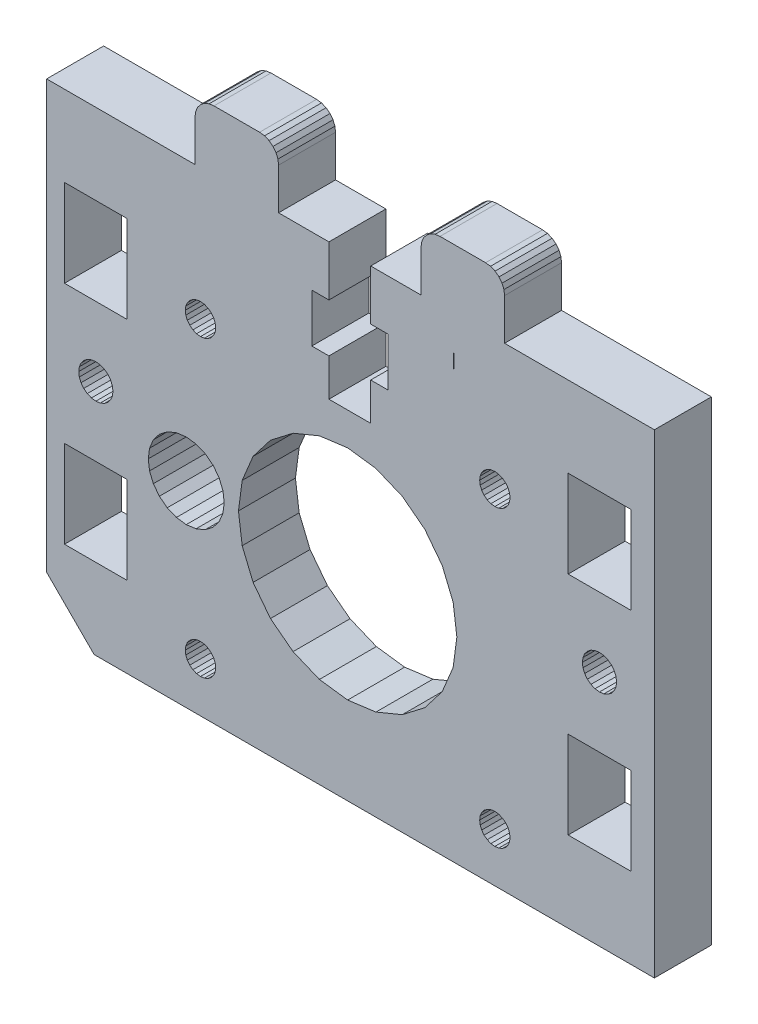
SolidWorks part; units mm, degrees
material "Maple"
ref_plane "Front Plane" through (0, 0, 0) normal (0, 0, 1) x (1, 0, 0)
ref_plane "Top Plane" through (0, 0, 0) normal (0, 1, 0) x (1, 0, 0)
ref_plane "Right Plane" through (0, 0, 0) normal (1, 0, 0) x (0, 0, -1)
sketch "Sketch1" plane through (0, 0, 0) normal (0, 0, 1) x (1, 0, 0)
  line L7685 (301.9537, 85.0925) -> (301.9537, 79.7925)
  line L7686 (267.8287, 40.0925) -> (272.8287, 35.0925)
  line L7687 (297.5537, 74.6925) -> (295.7537, 74.6925)
  line L7688 (316.0537, 85.0925) -> (316.0537, 89.4425)
  line L7689 (295.7537, 74.6925) -> (295.7537, 79.7925)
  line L7690 (307.2537, 85.0925) -> (301.9537, 85.0925)
  line L7691 (292.2537, 85.0925) -> (292.2537, 89.4425)
  line L7692 (329.3486, 76.5925) -> (329.3486, 67.3925)
  line L7693 (295.7537, 79.7925) -> (297.5537, 79.7925)
  line L7694 (329.3486, 67.3925) -> (322.7487, 67.3925)
  line L7695 (267.8287, 85.0925) -> (267.8287, 40.0925)
  line L7696 (301.9537, 79.7925) -> (303.7537, 79.7925)
  line L7697 (297.5537, 85.0925) -> (292.2537, 85.0925)
  line L7698 (303.7537, 74.6925) -> (301.9537, 74.6925)
  line L7699 (297.5537, 79.7925) -> (297.5537, 85.0925)
  line L7700 (303.7537, 79.7925) -> (303.7537, 74.6925)
  line L7701 (322.7487, 67.3925) -> (322.7487, 76.5925)
  line L7702 (322.7487, 76.5925) -> (329.3486, 76.5925)
  line L7703 (301.9537, 70.7425) -> (297.5537, 70.7425)
  line L7704 (297.5537, 70.7425) -> (297.5537, 74.6925)
  line L7705 (288.4205, 52.8161) -> (288.0287, 55.7925)
  line L7706 (283.6146, 72.838) -> (284.0287, 72.8925)
  line L7707 (301.9537, 74.6925) -> (301.9537, 70.7425)
  line L7708 (316.0537, 89.4425) -> (315.9855, 89.9601)
  line L7709 (315.9855, 89.9601) -> (315.7857, 90.4425)
  line L7710 (315.7857, 90.4425) -> (315.4679, 90.8567)
  line L7711 (315.4679, 90.8567) -> (315.0537, 91.1746)
  line L7712 (315.0537, 91.1746) -> (314.5713, 91.3744)
  line L7713 (314.0537, 91.4425) -> (309.2537, 91.4425)
  line L7714 (314.5713, 91.3744) -> (314.0537, 91.4425)
  line L7715 (283.4537, 89.4425) -> (283.4537, 85.0925)
  line L7716 (283.4537, 89.4425) -> (283.5218, 89.9601)
  line L7717 (283.5218, 89.9601) -> (283.7216, 90.4425)
  line L7718 (283.7216, 90.4425) -> (284.0395, 90.8567)
  line L7719 (284.0395, 90.8567) -> (284.4537, 91.1746)
  line L7720 (284.4537, 91.1746) -> (284.936, 91.3744)
  line L7721 (284.936, 91.3744) -> (285.4537, 91.4425)
  line L7722 (292.2537, 89.4425) -> (292.1855, 89.9601)
  line L7723 (292.1855, 89.9601) -> (291.9857, 90.4425)
  line L7724 (291.9857, 90.4425) -> (291.6679, 90.8567)
  line L7725 (291.6679, 90.8567) -> (291.2537, 91.1746)
  line L7726 (291.2537, 91.1746) -> (290.7713, 91.3744)
  line L7727 (290.2537, 91.4425) -> (285.4537, 91.4425)
  line L7728 (290.7713, 91.3744) -> (290.2537, 91.4425)
  line L7729 (307.2537, 89.4425) -> (307.2537, 85.0925)
  line L7730 (307.2537, 89.4425) -> (307.3218, 89.9601)
  line L7731 (307.3218, 89.9601) -> (307.5216, 90.4425)
  line L7732 (307.5216, 90.4425) -> (307.8394, 90.8567)
  line L7733 (307.8394, 90.8567) -> (308.2537, 91.1746)
  line L7734 (308.2537, 91.1746) -> (308.736, 91.3744)
  line L7735 (308.736, 91.3744) -> (309.2537, 91.4425)
  line L7736 (327.3227, 61.3665) -> (327.609, 60.9934)
  line L7737 (285.9928, 53.7925) -> (285.3571, 52.9641)
  line L7738 (315.4428, 69.747) -> (315.0287, 69.6925)
  line L7739 (285.16, 72.4239) -> (285.4143, 72.0925)
  line L7740 (288.4205, 58.7689) -> (289.5694, 61.5425)
  line L7741 (285.16, 70.1611) -> (284.8287, 69.9069)
  line L7742 (315.0287, 69.6925) -> (314.6145, 69.747)
  line L7743 (324.2469, 60.0925) -> (324.3083, 60.5588)
  line L7744 (324.4883, 60.9934) -> (324.7746, 61.3665)
  line L7745 (278.665, 54.7572) -> (278.5287, 55.7925)
  line L7746 (282.8973, 70.1611) -> (282.643, 70.4925)
  line L7747 (309.488, 61.5425) -> (310.6368, 58.7689)
  line L7748 (283.6146, 41.838) -> (284.0287, 41.8925)
  line L7749 (310.6368, 58.7689) -> (311.0287, 55.7925)
  line L7750 (324.7746, 61.3665) -> (325.1478, 61.6529)
  line L7751 (315.8287, 38.9069) -> (315.4428, 38.747)
  line L7752 (283.5639, 59.6562) -> (284.5287, 59.2566)
  line L7753 (310.6368, 52.8161) -> (309.488, 50.0425)
  line L7754 (326.515, 61.8328) -> (326.9495, 61.6529)
  line L7755 (326.0487, 58.2908) -> (325.5823, 58.3522)
  line L7756 (282.643, 70.4925) -> (282.4832, 70.8784)
  line L7757 (313.643, 70.4925) -> (313.4832, 70.8784)
  line L7758 (313.8973, 72.4239) -> (314.2287, 72.6782)
  line L7759 (327.3227, 58.8185) -> (326.9495, 58.5322)
  line L7760 (313.4832, 70.8784) -> (313.4287, 71.2925)
  line L7761 (325.1478, 61.6529) -> (325.5823, 61.8328)
  line L7762 (282.4287, 71.2925) -> (282.4832, 71.7066)
  line L7763 (293.7787, 45.8332) -> (291.3969, 47.6608)
  line L7764 (285.5741, 71.7066) -> (285.6287, 71.2925)
  line L7765 (289.5694, 50.0425) -> (288.4205, 52.8161)
  line L7766 (313.8973, 70.1611) -> (313.643, 70.4925)
  line L7767 (313.643, 41.0925) -> (313.8973, 41.4239)
  line L7768 (291.3969, 63.9242) -> (293.7787, 65.7518)
  line L7769 (325.1478, 58.5322) -> (324.7746, 58.8185)
  line L7770 (283.5639, 51.9288) -> (282.5287, 51.7925)
  line L7771 (281.4934, 51.9288) -> (280.5287, 52.3284)
  line L7772 (288.0287, 55.7925) -> (288.4205, 58.7689)
  line L7773 (283.2287, 72.6782) -> (283.6146, 72.838)
  line L7774 (269.7087, 67.3925) -> (269.7087, 76.5925)
  line L7775 (269.7087, 76.5925) -> (276.3087, 76.5925)
  line L7776 (276.3087, 76.5925) -> (276.3087, 67.3925)
  line L7777 (276.3087, 67.3925) -> (269.7087, 67.3925)
  line L7778 (276.3087, 52.7925) -> (276.3087, 43.5925)
  line L7779 (276.3087, 43.5925) -> (269.7087, 43.5925)
  line L7780 (314.2287, 41.6782) -> (314.6145, 41.838)
  line L7781 (282.8973, 41.4239) -> (283.2287, 41.6782)
  line L7782 (326.515, 58.3522) -> (326.0487, 58.2908)
  line L7783 (271.2683, 60.5588) -> (271.4483, 60.9934)
  line L7784 (316.16, 41.4239) -> (316.4143, 41.0925)
  line L7785 (313.8973, 39.1612) -> (313.643, 39.4925)
  line L7786 (326.9495, 58.5322) -> (326.515, 58.3522)
  line L7787 (302.5051, 66.9007) -> (305.2787, 65.7518)
  line L7788 (284.4428, 69.747) -> (284.0287, 69.6925)
  line L7789 (326.9495, 61.6529) -> (327.3227, 61.3665)
  line L7790 (327.8504, 60.0925) -> (327.789, 59.6262)
  line L7791 (272.5423, 58.3522) -> (272.1078, 58.5322)
  line L7792 (315.0287, 41.8925) -> (315.4428, 41.838)
  line L7793 (296.5522, 66.9007) -> (299.5287, 67.2925)
  line L7794 (278.665, 56.8278) -> (279.0646, 57.7925)
  line L7795 (291.3969, 47.6608) -> (289.5694, 50.0425)
  line L7796 (285.16, 39.1612) -> (284.8287, 38.9069)
  line L7797 (282.643, 41.0925) -> (282.8973, 41.4239)
  line L7798 (284.0287, 72.8925) -> (284.4428, 72.838)
  line L7799 (282.4832, 71.7066) -> (282.643, 72.0925)
  line L7800 (315.0287, 38.6925) -> (314.6145, 38.747)
  line L7801 (324.3083, 59.6262) -> (324.2469, 60.0925)
  line L7802 (285.3571, 58.6209) -> (285.9928, 57.7925)
  line L7803 (316.16, 72.4239) -> (316.4143, 72.0925)
  line L7804 (279.7002, 58.6209) -> (280.5287, 59.2566)
  line L7805 (326.0487, 61.8942) -> (326.515, 61.8328)
  line L7806 (315.4428, 41.838) -> (315.8287, 41.6782)
  line L7807 (283.2287, 69.9069) -> (282.8973, 70.1611)
  line L7808 (271.7347, 61.3665) -> (272.1078, 61.6529)
  line L7809 (282.4832, 70.8784) -> (282.4287, 71.2925)
  line L7810 (274.749, 59.6262) -> (274.569, 59.1917)
  line L7811 (271.4483, 59.1917) -> (271.2683, 59.6262)
  line L7812 (307.6604, 63.9242) -> (309.488, 61.5425)
  line L7813 (315.4428, 72.838) -> (315.8287, 72.6782)
  line L7814 (285.5741, 70.8784) -> (285.4143, 70.4925)
  line L7815 (285.4143, 70.4925) -> (285.16, 70.1611)
  line L7816 (314.2287, 38.9069) -> (313.8973, 39.1612)
  line L7817 (314.2287, 69.9069) -> (313.8973, 70.1611)
  line L7818 (272.1078, 58.5322) -> (271.7347, 58.8185)
  line L7819 (285.4143, 41.0925) -> (285.5741, 40.7066)
  line L7820 (284.8287, 69.9069) -> (284.4428, 69.747)
  line L7821 (313.643, 39.4925) -> (313.4832, 39.8784)
  line L7822 (284.8287, 38.9069) -> (284.4428, 38.747)
  line L7823 (286.5287, 55.7925) -> (286.3924, 54.7572)
  line L7824 (282.8973, 39.1612) -> (282.643, 39.4925)
  line L7825 (314.2287, 72.6782) -> (314.6145, 72.838)
  line L7826 (315.8287, 41.6782) -> (316.16, 41.4239)
  line L7827 (283.6146, 38.747) -> (283.2287, 38.9069)
  line L7828 (316.5741, 40.7066) -> (316.6287, 40.2925)
  line L7829 (316.6287, 71.2925) -> (316.5741, 70.8784)
  line L7830 (274.569, 60.9934) -> (274.749, 60.5588)
  line L7831 (271.2069, 60.0925) -> (271.2683, 60.5588)
  line L7832 (299.5287, 44.2925) -> (296.5522, 44.6844)
  line L7833 (282.4287, 40.2925) -> (282.4832, 40.7066)
  line L7834 (324.7746, 58.8185) -> (324.4883, 59.1917)
  line L7835 (325.5823, 61.8328) -> (326.0487, 61.8942)
  line L7836 (327.609, 60.9934) -> (327.789, 60.5588)
  line L7837 (316.4143, 72.0925) -> (316.5741, 71.7066)
  line L7838 (316.5741, 71.7066) -> (316.6287, 71.2925)
  line L7839 (284.4428, 72.838) -> (284.8287, 72.6782)
  line L7840 (316.5741, 39.8784) -> (316.4143, 39.4925)
  line L7841 (305.2787, 65.7518) -> (307.6604, 63.9242)
  line L7842 (284.0287, 41.8925) -> (284.4428, 41.838)
  line L7843 (324.3083, 60.5588) -> (324.4883, 60.9934)
  line L7844 (316.4143, 41.0925) -> (316.5741, 40.7066)
  line L7845 (282.5287, 51.7925) -> (281.4934, 51.9288)
  line L7846 (286.3924, 56.8278) -> (286.5287, 55.7925)
  line L7847 (284.4428, 38.747) -> (284.0287, 38.6925)
  line L7848 (278.5287, 55.7925) -> (278.665, 56.8278)
  line L7849 (316.5741, 70.8784) -> (316.4143, 70.4925)
  line L7850 (315.8287, 72.6782) -> (316.16, 72.4239)
  line L7851 (315.0287, 72.8925) -> (315.4428, 72.838)
  line L7852 (313.4832, 71.7066) -> (313.643, 72.0925)
  line L7853 (313.643, 72.0925) -> (313.8973, 72.4239)
  line L7854 (282.4832, 39.8784) -> (282.4287, 40.2925)
  line L7855 (279.7002, 52.9641) -> (279.0646, 53.7925)
  line L7856 (315.8287, 69.9069) -> (315.4428, 69.747)
  line L7857 (289.5694, 61.5425) -> (291.3969, 63.9242)
  line L7858 (293.7787, 65.7518) -> (296.5522, 66.9007)
  line L7859 (299.5287, 67.2925) -> (302.5051, 66.9007)
  line L7860 (311.0287, 55.7925) -> (310.6368, 52.8161)
  line L7861 (309.488, 50.0425) -> (307.6604, 47.6608)
  line L7862 (307.6604, 47.6608) -> (305.2787, 45.8332)
  line L7863 (305.2787, 45.8332) -> (302.5051, 44.6844)
  line L7864 (302.5051, 44.6844) -> (299.5287, 44.2925)
  line L7865 (296.5522, 44.6844) -> (293.7787, 45.8332)
  line L7866 (284.8287, 72.6782) -> (285.16, 72.4239)
  line L7867 (285.4143, 72.0925) -> (285.5741, 71.7066)
  line L7868 (285.6287, 71.2925) -> (285.5741, 70.8784)
  line L7869 (284.0287, 69.6925) -> (283.6146, 69.747)
  line L7870 (283.6146, 69.747) -> (283.2287, 69.9069)
  line L7871 (282.643, 72.0925) -> (282.8973, 72.4239)
  line L7872 (282.8973, 72.4239) -> (283.2287, 72.6782)
  line L7873 (327.789, 60.5588) -> (327.8504, 60.0925)
  line L7874 (327.789, 59.6262) -> (327.609, 59.1917)
  line L7875 (327.609, 59.1917) -> (327.3227, 58.8185)
  line L7876 (325.5823, 58.3522) -> (325.1478, 58.5322)
  line L7877 (324.4883, 59.1917) -> (324.3083, 59.6262)
  line L7878 (285.3571, 52.9641) -> (284.5287, 52.3284)
  line L7879 (284.5287, 52.3284) -> (283.5639, 51.9288)
  line L7880 (280.5287, 52.3284) -> (279.7002, 52.9641)
  line L7881 (279.0646, 53.7925) -> (278.665, 54.7572)
  line L7882 (279.0646, 57.7925) -> (279.7002, 58.6209)
  line L7883 (280.5287, 59.2566) -> (281.4934, 59.6562)
  line L7884 (281.4934, 59.6562) -> (282.5287, 59.7925)
  line L7885 (282.5287, 59.7925) -> (283.5639, 59.6562)
  line L7886 (284.5287, 59.2566) -> (285.3571, 58.6209)
  line L7887 (285.9928, 57.7925) -> (286.3924, 56.8278)
  line L7888 (286.3924, 54.7572) -> (285.9928, 53.7925)
  line L7889 (314.6145, 69.747) -> (314.2287, 69.9069)
  line L7890 (313.4287, 71.2925) -> (313.4832, 71.7066)
  line L7891 (314.6145, 72.838) -> (315.0287, 72.8925)
  line L7892 (316.4143, 70.4925) -> (316.16, 70.1611)
  line L7893 (316.16, 70.1611) -> (315.8287, 69.9069)
  line L7894 (284.4428, 41.838) -> (284.8287, 41.6782)
  line L7895 (284.8287, 41.6782) -> (285.16, 41.4239)
  line L7896 (285.16, 41.4239) -> (285.4143, 41.0925)
  line L7897 (285.5741, 40.7066) -> (285.6287, 40.2925)
  line L7898 (285.6287, 40.2925) -> (285.5741, 39.8784)
  line L7899 (285.5741, 39.8784) -> (285.4143, 39.4925)
  line L7900 (285.4143, 39.4925) -> (285.16, 39.1612)
  line L7901 (284.0287, 38.6925) -> (283.6146, 38.747)
  line L7902 (283.2287, 38.9069) -> (282.8973, 39.1612)
  line L7903 (282.643, 39.4925) -> (282.4832, 39.8784)
  line L7904 (282.4832, 40.7066) -> (282.643, 41.0925)
  line L7905 (283.2287, 41.6782) -> (283.6146, 41.838)
  line L7906 (315.4428, 38.747) -> (315.0287, 38.6925)
  line L7907 (314.6145, 38.747) -> (314.2287, 38.9069)
  line L7908 (313.4832, 39.8784) -> (313.4287, 40.2925)
  line L7909 (313.4287, 40.2925) -> (313.4832, 40.7066)
  line L7910 (313.4832, 40.7066) -> (313.643, 41.0925)
  line L7911 (313.8973, 41.4239) -> (314.2287, 41.6782)
  line L7912 (314.6145, 41.838) -> (315.0287, 41.8925)
  line L7913 (316.6287, 40.2925) -> (316.5741, 39.8784)
  line L7914 (316.4143, 39.4925) -> (316.16, 39.1612)
  line L7915 (316.16, 39.1612) -> (315.8287, 38.9069)
  line L7916 (269.7087, 43.5925) -> (269.7087, 52.7925)
  line L7917 (269.7087, 52.7925) -> (276.3087, 52.7925)
  line L7918 (271.4483, 60.9934) -> (271.7347, 61.3665)
  line L7919 (272.1078, 61.6529) -> (272.5423, 61.8328)
  line L7920 (272.5423, 61.8328) -> (273.0087, 61.8942)
  line L7921 (273.0087, 61.8942) -> (273.475, 61.8328)
  line L7922 (273.475, 61.8328) -> (273.9095, 61.6529)
  line L7923 (273.9095, 61.6529) -> (274.2827, 61.3665)
  line L7924 (274.2827, 61.3665) -> (274.569, 60.9934)
  line L7925 (274.749, 60.5588) -> (274.8104, 60.0925)
  line L7926 (274.8104, 60.0925) -> (274.749, 59.6262)
  line L7927 (274.569, 59.1917) -> (274.2827, 58.8185)
  line L7928 (274.2827, 58.8185) -> (273.9095, 58.5322)
  line L7929 (273.9095, 58.5322) -> (273.475, 58.3522)
  line L7930 (273.475, 58.3522) -> (273.0087, 58.2908)
  line L7931 (273.0087, 58.2908) -> (272.5423, 58.3522)
  line L7932 (271.7347, 58.8185) -> (271.4483, 59.1917)
  line L7933 (271.2683, 59.6262) -> (271.2069, 60.0925)
  line L7934 (329.3486, 52.7925) -> (329.3486, 43.5925)
  line L7935 (329.3486, 43.5925) -> (322.7487, 43.5925)
  line L7936 (322.7487, 43.5925) -> (322.7487, 52.7925)
  line L7937 (322.7487, 52.7925) -> (329.3486, 52.7925)
  line L8452 (331.8286, 85.0925) -> (316.0537, 85.0925)
  line L8453 (331.8287, 35.0925) -> (331.8286, 85.0925)
  line L8454 (272.8287, 35.0925) -> (331.8287, 35.0925)
  line L8455 (283.4537, 85.0925) -> (267.8287, 85.0925)
  line L9715 (310.6977, 81.5005) -> (310.7178, 81.5967)
  line L9716 (310.7178, 81.5967) -> (310.7781, 81.6855)
  line L9717 (310.7781, 81.6855) -> (311.0192, 81.8408)
  line L9718 (311.0192, 81.8408) -> (311.3806, 81.9462)
  line L9719 (311.3806, 81.9462) -> (311.8216, 81.9813)
  line L9720 (311.8216, 81.9813) -> (312.2626, 81.9462)
  line L9721 (312.2626, 81.9462) -> (312.6239, 81.8408)
  line L9722 (312.6239, 81.8408) -> (312.8651, 81.6855)
  line L9723 (312.8651, 81.6855) -> (312.9254, 81.5967)
  line L9724 (312.9254, 81.5967) -> (312.9455, 81.5005)
  line L9725 (312.9455, 81.5005) -> (312.9455, 78.1541)
  line L9726 (312.9455, 78.1541) -> (312.9254, 78.0579)
  line L9727 (312.9254, 78.0579) -> (312.8651, 77.9692)
  line L9728 (312.8651, 77.9692) -> (312.6239, 77.8138)
  line L9729 (312.6239, 77.8138) -> (312.2626, 77.7085)
  line L9730 (312.2626, 77.7085) -> (311.8216, 77.6734)
  line L9731 (311.8216, 77.6734) -> (311.3806, 77.7085)
  line L9732 (311.3806, 77.7085) -> (311.0192, 77.8138)
  line L9733 (311.0192, 77.8138) -> (310.7781, 77.9692)
  line L9734 (310.7781, 77.9692) -> (310.7178, 78.0579)
  line L9735 (310.7178, 78.0579) -> (310.6977, 78.1541)
  line L9736 (310.6977, 78.1541) -> (310.6977, 78.46)
  line L9737 (310.6977, 78.46) -> (310.6977, 78.1541)
  line L9738 (310.6977, 78.1541) -> (310.7178, 78.0579)
  line L9739 (310.7178, 78.0579) -> (310.7781, 77.9692)
  line L9740 (310.7781, 77.9692) -> (311.0192, 77.8138)
  line L9741 (311.0192, 77.8138) -> (311.3806, 77.7085)
  line L9742 (311.3806, 77.7085) -> (311.8216, 77.6734)
  line L9743 (311.8216, 77.6734) -> (312.2626, 77.7085)
  line L9744 (312.2626, 77.7085) -> (312.6239, 77.8138)
  line L9745 (312.6239, 77.8138) -> (312.8651, 77.9692)
  line L9746 (312.8651, 77.9692) -> (312.9254, 78.0579)
  line L9747 (312.9254, 78.0579) -> (312.9455, 78.1541)
  line L9748 (312.9455, 78.1541) -> (312.9455, 81.5005)
  line L9749 (312.9455, 81.5005) -> (312.9254, 81.5967)
  line L9750 (312.9254, 81.5967) -> (312.8651, 81.6855)
  line L9751 (312.8651, 81.6855) -> (312.6239, 81.8408)
  line L9752 (312.6239, 81.8408) -> (312.2626, 81.9462)
  line L9753 (312.2626, 81.9462) -> (311.8216, 81.9813)
  line L9754 (311.8216, 81.9813) -> (311.3806, 81.9462)
  line L9755 (311.3806, 81.9462) -> (311.0192, 81.8408)
  line L9756 (311.0192, 81.8408) -> (310.7781, 81.6855)
  line L9757 (310.7781, 81.6855) -> (310.7178, 81.5967)
  line L9758 (310.7178, 81.5967) -> (310.6977, 79.8273)
  line L9759 (310.6977, 79.8273) -> (311.8091, 79.8273)
  line L9760 (311.8091, 79.8273) -> (310.6977, 79.8273)
  line L9761 (310.6977, 79.8273) -> (310.6977, 81.5005)
extrude "Boss-Extrude1" add sketch "Sketch1" along normal blind 6 contours L7715 L8455 L7695 L7686 L8454 L8453 L8452 L7688 L7708 L7709 L7710 L7711 L7712 L7714 L7713 L7735 L7734 L7733 L7732 L7731 L7730 L7729 L7690 L7685 L7696 L7700 L7698 L7707 L7703 L7704 L7687 L7689 L7693 L7699 L7697 L7691 L7722 L7723 L7724 L7725 L7726 L7728 L7727 L7721 L7720 L7719 L7718 L7717 L7716 L7811
